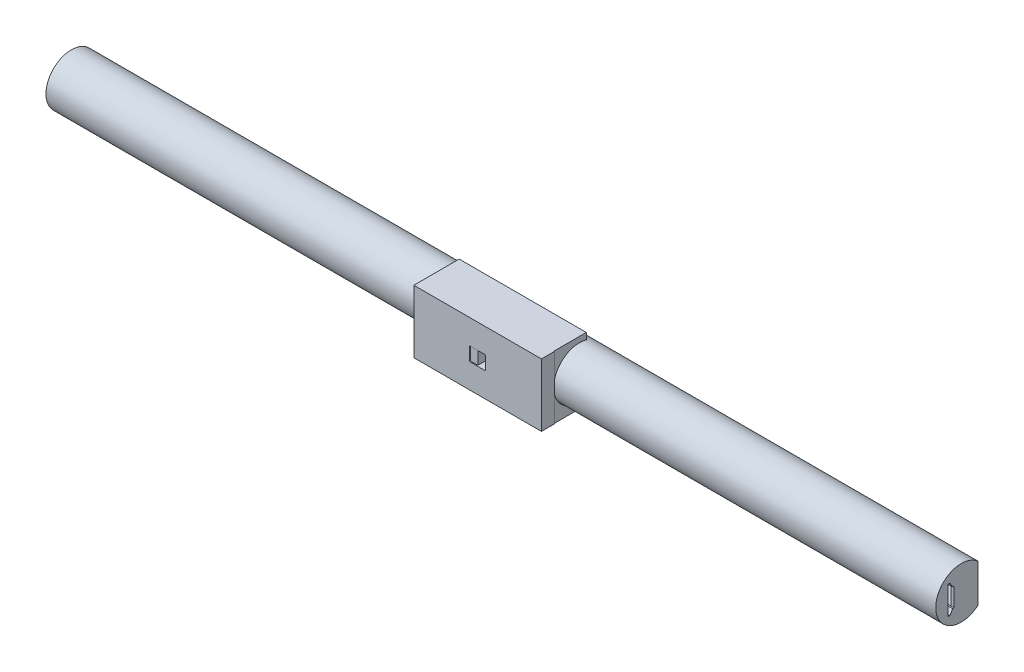
SolidWorks part; units mm, degrees
ref_plane "Front Plane" through (0, 0, 0) normal (0, 0, 1) x (1, 0, 0)
ref_plane "Top Plane" through (0, 0, 0) normal (0, 1, 0) x (1, 0, 0)
ref_plane "Right Plane" through (0, 0, 0) normal (1, 0, 0) x (0, 0, -1)
sketch "NewBarProfile" plane through (0, 0, 0) normal (1, 0, 0) x (0, 1, 0)
  line L0 (7.5, -6.6144) -> (-7.5, -6.6144) construction
  line L1 (-7.5, -6.6144) -> (-6.3, -6.6144)
  line L2 (-6.3, -6.6144) -> (-6.3, 1.2617)
  line L3 (-6.3, 1.2617) -> (0, 4.899) construction
  line L4 (5, 4.899) -> (-5, 4.899) construction
  line L5 (0, -14.4444) -> (0, 14.4444) construction
  line L6 (-5.5, 5.199) -> (5.5, 5.199)
  line L7 (-6.3, 1.2617) -> (-3.7026, 2.7613)
  line L8 (0, 0) -> (-7.1429, 6.9985) construction
  line L9 (-5.5, 4.399) -> (-3.7026, 3.3613)
  line L10 (-5.5, 5.199) -> (-5.5, 4.399)
  line L11 (-3.7026, 3.3613) -> (-3.7026, 2.7613)
  line L12 (7.5, -6.6144) -> (6.3, -6.6144)
  line L13 (3.7026, 3.3613) -> (3.7026, 2.7613)
  line L14 (5.5, 5.199) -> (5.5, 4.399)
  line L15 (5.5, 4.399) -> (3.7026, 3.3613)
  line L16 (6.3, 1.2617) -> (3.7026, 2.7613)
  line L17 (6.3, -6.6144) -> (6.3, 1.2617)
  line L18 (0, -14.4444) -> (0, 14.4444) construction
  circle A0 centre (0, 0) radius 10 construction
  arc A1 (-7.5, -6.6144) -> (7.5, -6.6144) centre (0, 0) cw
  point P11 (0, 4.899)
  point P14 (0, 0)
sketch "Sketch5" plane through (0, 0, 3.7) normal (1, 0, 0) x (0, 1, 0)
  line L0 (0, -16.5814) -> (0, 9.1814) construction
  line L5 (-7.5, -2.6947) -> (-6.4, -4.6) construction
  line L6 (7.5, -2.6947) -> (6.4, -4.6) construction
  line L7 (5.3668, 1) -> (7.5, -2.6947) construction
  line L8 (-5.3668, 1) -> (5.3668, 1) construction
  line L9 (-5.3668, 1) -> (-7.5, -2.6947) construction
  line L10 (7.7309, -2.6947) -> (6.5732, -4.7)
  line L11 (5.4823, 1.2) -> (7.7309, -2.6947)
  line L12 (-5.4823, 1.2) -> (5.4823, 1.2)
  line L13 (-5.4823, 1.2) -> (-7.7309, -2.6947)
  line L14 (-7.7309, -2.6947) -> (-6.5732, -4.7)
  line L15 (-6.5732, -4.7) -> (6.5732, -4.7)
  line L17 (0, -9.7207) -> (0, 9.7207) construction
  line L18 (-6.9, -10.9381) -> (6.9, -10.9381)
  line L19 (0, -10.9381) -> (0, -3.7) construction
  circle A0 centre (0, -3.7) radius 10 construction
  arc A1 (-6.9, -10.9381) -> (6.9, -10.9381) centre (0, -3.7) cw
  point P18 (0, -13.7)
sketch "Sketch8" plane through (0, 0, 3.7) normal (0, -1, 0) x (1, 0, 0)
  line L2 (0, -9.7207) -> (-145, -9.7207)
  line L3 (0, -9.9381) -> (-145, -9.9381)
  line L4 (0, -10.9381) -> (-150, -10.9381)
  point P0 (0, -9.7207)
  point P3 (0, -10.9381)
sketch "Sketch9" plane through (0, 0, 3.7) normal (1, 0, 0) x (0, 1, 0)
  line L0 (-6.9, -10.9381) -> (6.9, -10.9381) construction
  line L3 (-6.9, -10.9381) -> (6.9, -10.9381) construction
  line L4 (-6.4874, -9.9381) -> (6.4874, -9.9381)
  line L5 (-6.4017, -9.7381) -> (6.4017, -9.7381)
  arc A3 (6.9, -10.9381) -> (-6.9, -10.9381) centre (0, -3.7) ccw construction
  arc A4 (6.4874, -9.9381) -> (-6.4874, -9.9381) centre (0, -3.7) ccw
  arc A5 (6.4017, -9.7381) -> (-6.4017, -9.7381) centre (0, -3.7) ccw
sketch "Sketch1" plane through (0, 0, 0) normal (1, 0, 0) x (0, 0, -1)
  line L63 (-5.199, 5.5) -> (-4.399, 5.5)
  line L64 (-4.399, 5.5) -> (-3.3613, 3.7026)
  line L65 (-3.3613, 3.7026) -> (-2.7613, 3.7026)
  line L66 (-2.7613, 3.7026) -> (-1.2617, 6.3)
  line L67 (-1.2617, 6.3) -> (6.6144, 6.3)
  line L68 (6.6144, 6.3) -> (6.6144, 7.5)
  line L69 (6.6144, -7.5) -> (6.6144, -6.3)
  line L70 (6.6144, -6.3) -> (-1.2617, -6.3)
  line L71 (-1.2617, -6.3) -> (-2.7613, -3.7026)
  line L72 (-2.7613, -3.7026) -> (-3.3613, -3.7026)
  line L73 (-3.3613, -3.7026) -> (-4.399, -5.5)
  line L74 (-4.399, -5.5) -> (-5.199, -5.5)
  line L75 (-5.199, -5.5) -> (-5.199, 5.5)
  line L76 (-5.199, 5.5) -> (-4.399, 5.5)
  line L77 (-4.399, 5.5) -> (-3.3613, 3.7026)
  line L78 (-3.3613, 3.7026) -> (-2.7613, 3.7026)
  line L79 (-2.7613, 3.7026) -> (-1.2617, 6.3)
  line L80 (-1.2617, 6.3) -> (6.6144, 6.3)
  line L81 (6.6144, 6.3) -> (6.6144, 7.5)
  line L82 (6.6144, -7.5) -> (6.6144, -6.3)
  line L83 (6.6144, -6.3) -> (-1.2617, -6.3)
  line L84 (-1.2617, -6.3) -> (-2.7613, -3.7026)
  line L85 (-2.7613, -3.7026) -> (-3.3613, -3.7026)
  line L86 (-3.3613, -3.7026) -> (-4.399, -5.5)
  line L87 (-4.399, -5.5) -> (-5.199, -5.5)
  line L88 (-5.199, -5.5) -> (-5.199, 5.5)
  arc A9 (6.6144, 7.5) -> (6.6144, -7.5) centre (0, 0) ccw
  arc A10 (6.6144, 7.5) -> (6.6144, -7.5) centre (0, 0) ccw
  dimension "D1" = 0
extrude "Bar" add sketch "Sketch1" against normal mid plane 350
sketch "Sketch13" plane through (0, 0, -6.6144) normal (0, 0, -1) x (-1, 0, 0)
  line L0 (175, 7.5) -> (175, -7.5)
  line L1 (175, -7.5) -> (173.8, -7.5)
  line L2 (175, -7.5) -> (-175, -7.5) construction
  line L3 (173.8, -7.5) -> (173.8, 7.5)
  line L4 (175, 7.5) -> (-175, 7.5) construction
  line L5 (173.8, 7.5) -> (175, 7.5)
  line L6 (125.4, 7.5) -> (124.6, 7.5)
  line L7 (124.6, 7.5) -> (124.6, -7.5)
  line L8 (124.6, -7.5) -> (125.4, -7.5)
  line L9 (125.4, -7.5) -> (125.4, 7.5)
  line L10 (125, 7.5) -> (125, -7.5) construction
  line L11 (75.4, -7.5) -> (75.4, 7.5)
  line L12 (75.4, 7.5) -> (74.6, 7.5)
  line L13 (74.6, 7.5) -> (74.6, -7.5)
  line L14 (74.6, -7.5) -> (75.4, -7.5)
  line L15 (25.4, -7.5) -> (25.4, 7.5)
  line L16 (25.4, 7.5) -> (24.6, 7.5)
  line L17 (24.6, 7.5) -> (24.6, -7.5)
  line L18 (24.6, -7.5) -> (25.4, -7.5)
  line L19 (-24.6, -7.5) -> (-24.6, 7.5)
  line L20 (-24.6, 7.5) -> (-25.4, 7.5)
  line L21 (-25.4, 7.5) -> (-25.4, -7.5)
  line L22 (-25.4, -7.5) -> (-24.6, -7.5)
  line L23 (-74.6, -7.5) -> (-74.6, 7.5)
  line L24 (-74.6, 7.5) -> (-75.4, 7.5)
  line L25 (-75.4, 7.5) -> (-75.4, -7.5)
  line L26 (-75.4, -7.5) -> (-74.6, -7.5)
  line L27 (-124.6, -7.5) -> (-124.6, 7.5)
  line L28 (-124.6, 7.5) -> (-125.4, 7.5)
  line L29 (-125.4, 7.5) -> (-125.4, -7.5)
  line L30 (-125.4, -7.5) -> (-124.6, -7.5)
  line L31 (0, -34.8434) -> (0, 34.8434) construction
  line L32 (-173.8, -7.5) -> (-173.8, 7.5)
  line L33 (-175, -7.5) -> (-173.8, -7.5)
  line L34 (-175, 7.5) -> (-175, -7.5)
  line L35 (-173.8, 7.5) -> (-175, 7.5)
  point P40 (0, 0)
  dimension "D1" = 1.2
  dimension "D2" = 0.8
  dimension "D3" = 50
  dimension "D5" = 50
  dimension "D4" = 6
extrude "Boss-Extrude1" add sketch "Sketch13" against normal up to vertex (9.3756 mm away) up to point (175, 3.7026, 2.7613)
sketch "Sketch14" plane through (0, 0, 0) normal (0, 1, 0) x (1, 0, 0)
  line L0 (0, 19.6952) -> (0, -19.6952) construction
  line L2 (-175, -10) -> (175, -10) construction
  line L3 (0.1, 6.6144) -> (-0.1, 6.6144)
  line L5 (0.1, 6.6144) -> (0.1, -10)
  line L7 (0.1, -10) -> (-0.1, -10)
  line L8 (-0.1, 6.6144) -> (-0.1, -10)
  line L9 (0.1, 6.6144) -> (-0.1, -10) construction
  line L10 (0.1, -10) -> (-0.1, 6.6144) construction
  line L11 (-175, 6.6144) -> (175, 6.6144) construction
  point P0 (0, -1.6928)
  point P3 (0, 0)
  dimension "D1" = 0.2
extrude "Cut-Extrude1" cut sketch "Sketch14" against normal through all both and the other way through all
sketch "Sketch15" plane through (0, 0, 0) normal (0, 1, 0) x (1, 0, 0)
  line L0 (-0.1, -8) -> (-0.1, -15)
  line L1 (-0.1, -15) -> (-3.1, -15)
  line L2 (-3.1, -15) -> (-10.1, -8)
  line L3 (-10.1, -8) -> (-0.1, -8)
  point P3 (-0.1, -10)
  dimension "D1" = 2
  dimension "D2" = 5
  dimension "D3" = 45
  dimension "D4" = 3
extrude "Boss-Extrude2" add sketch "Sketch15" along normal mid plane 5
sketch "Sketch16" plane through (-0.1, 0, 0) normal (1, 0, 0) x (0, 0, -1)
  line L48 (2.64, 9.8524) -> (2.64, 12.3524)
  line L49 (2.64, 12.3524) -> (-15.2, 12.3524)
  line L50 (-15.2, 12.3524) -> (-15.2, 2.7)
  line L51 (2.64, 9.8524) -> (8.4798, 8.2877)
  line L52 (-12.3198, 0) -> (12.3198, 0) construction
  line L53 (-15.2, -12.3524) -> (-15.2, -2.7)
  line L54 (2.64, -12.3524) -> (-15.2, -12.3524)
  line L55 (2.64, -9.8524) -> (2.64, -12.3524)
  line L56 (-9.8362, -2.7) -> (-15.2, -2.7)
  line L64 (-9.8362, 2.7) -> (-15.2, 2.7)
  line L65 (-15.2, 2.7) -> (-15.2, -2.7)
  line L66 (-15.2, -2.7) -> (-9.8362, -2.7)
  line L67 (6.8144, -7.5897) -> (6.8144, -6.1)
  line L68 (6.8144, -6.1) -> (-1.1462, -6.1)
  line L69 (-1.1462, -6.1) -> (-2.6458, -3.5026)
  line L70 (-2.6458, -3.5026) -> (-3.4767, -3.5026)
  line L71 (-3.4767, -3.5026) -> (-4.5144, -5.3)
  line L72 (-4.5144, -5.3) -> (-4.999, -5.3)
  line L73 (-4.999, -5.3) -> (-4.999, 5.3)
  line L74 (-4.999, 5.3) -> (-4.5144, 5.3)
  line L75 (-4.5144, 5.3) -> (-3.4767, 3.5026)
  line L76 (-3.4767, 3.5026) -> (-2.6458, 3.5026)
  line L77 (-2.6458, 3.5026) -> (-1.1462, 6.1)
  line L78 (-1.1462, 6.1) -> (6.8144, 6.1)
  line L79 (6.8144, 6.1) -> (6.8144, 7.5897)
  line L80 (-9.8362, 2.7) -> (-15.2, 2.7)
  arc A6 (-9.8362, 2.7) -> (2.64, 9.8524) centre (0, 0) cw
  arc A7 (-9.8362, -2.7) -> (2.64, -9.8524) centre (0, 0) ccw
  arc A8 (6.8144, 7.5897) -> (-9.8362, 2.7) centre (0, 0) ccw
  arc A9 (-9.8362, -2.7) -> (6.8144, -7.5897) centre (0, 0) ccw
  arc A10 (6.8144, 7.5897) -> (-9.8362, 2.7) centre (0, 0) ccw construction
  point P7 (0, 0)
  dimension "D2" = 105
  dimension "D3" = 2.5
  dimension "D1" = 0.2
extrude "Boss-Extrude3" add sketch "Sketch16" along normal mid plane 50 separate body contours A7 L56 L53 L54 L55 | L80 A6 L48 L49 L50
sketch "Sketch17" plane through (0, 0, 0) normal (0, 1, 0) x (1, 0, 0)
  line L0 (-25.1, -10.1) -> (-8.2828, -10.1)
  line L2 (-8.2828, -10.1) -> (0, -10.1) construction
  line L4 (-25.1, -15.2) -> (-3.1828, -15.2)
  line L5 (-3.1828, -15.2) -> (-8.2828, -10.1)
  line L7 (0, -19.9979) -> (0, 19.9979) construction
  line L8 (0.1, -15.2) -> (0.1, -7.8)
  line L9 (-3.1828, -15.2) -> (0.1, -15.2)
  line L10 (-10.5828, -7.8) -> (-3.1828, -15.2)
  line L11 (0.1, -7.8) -> (-10.5828, -7.8)
  line L12 (0.1, -15.2) -> (0.1, -7.8) construction
  line L13 (-3.1828, -15.2) -> (0.1, -15.2) construction
  line L14 (-10.5828, -7.8) -> (-3.1828, -15.2) construction
  line L15 (0.1, -7.8) -> (-10.5828, -7.8) construction
  line L16 (-25.1, -9.8362) -> (-25.1, -15.2)
  line L17 (-25.1, -15.2) -> (24.9, -15.2)
  line L18 (24.9, -15.2) -> (24.9, -9.8362)
  line L19 (24.9, -9.8362) -> (-25.1, -9.8362)
  line L20 (-25.1, -10.1) -> (-25.1, -15.2)
  line L24 (8.2828, -10.1) -> (25.1, -10.1)
  line L25 (3.1828, -15.2) -> (8.2828, -10.1)
  line L26 (25.1, -15.2) -> (3.1828, -15.2)
  line L27 (25.1, -10.1) -> (25.1, -15.2)
  circle A0 centre (0, 0) radius 10.1 construction
  point P12 (0, 0)
  dimension "D3" = 20.2
  dimension "D1" = 0.2
  dimension "D2" = 0
extrude "Boss-Extrude4" add sketch "Sketch17" along normal through all and the other way through all
sketch "Sketch18" plane through (0, 0, -6.6144) normal (0, 0, -1) x (-1, 0, 0)
  line L0 (0.1, 7.5) -> (0.1, -7.5)
  line L1 (0.1, -7.5) -> (1.3, -7.5)
  line L2 (175, -7.5) -> (0.1, -7.5) construction
  line L3 (1.3, -7.5) -> (1.3, 7.5)
  line L4 (175, 7.5) -> (0.1, 7.5) construction
  line L5 (1.3, 7.5) -> (0.1, 7.5)
  dimension "D1" = 1.2
extrude "Boss-Extrude5" add sketch "Sketch18" against normal blind 0.2
